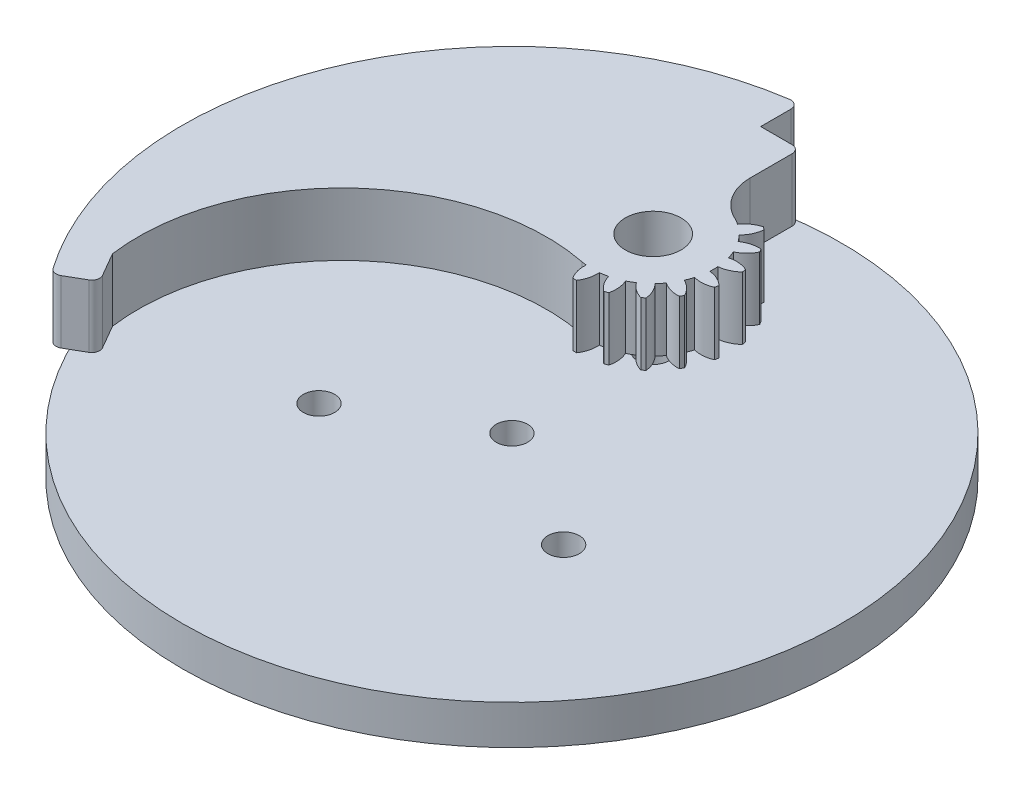
SolidWorks part; units mm, degrees
material "PE Low Density Film"
ref_plane "Front Plane" through (0, 0, 0) normal (0, 0, 1) x (1, 0, 0)
ref_plane "Top Plane" through (0, 0, 0) normal (0, 1, 0) x (1, 0, 0)
ref_plane "Right Plane" through (0, 0, 0) normal (1, 0, 0) x (0, 0, -1)
sketch "Sketch2" plane through (0, 0, 0) normal (0, 1, 0) x (1, 0, 0)
  line L0 (0, 18) -> (0, 0) construction
  line L1 (0, 0) -> (0, 18) construction
  circle A0 centre (0, 0) radius 42
  circle A1 centre (0, 0) radius 2
  circle A2 centre (0, 18) radius 2
  circle A3 centre (15.5885, -9) radius 2
  circle A4 centre (-15.5885, -9) radius 2
  dimension "D1" = 84
  dimension "D2" = 4
  dimension "D3" = 4
  dimension "D4" = 18
  dimension "D5" = 3
extrude "Boss-Extrude1" add sketch "Sketch2" along normal blind 5
sketch "Sketch3" plane through (0, 5, 0) normal (0, 1, 0) x (1, 0, 0)
  line L0 (0, 0) -> (0, 18) construction
sketch "Sketch5" plane through (0, 5, 0) normal (0, 1, 0) x (1, 0, 0)
  arc A72 (6.2374, 25.8163) -> (4.3083, 24.4409) centre (7.2464, 22.3606) ccw
  arc A73 (4.3083, 24.4409) -> (3.4238, 24.9516) centre (0, 18) ccw
  arc A74 (3.4238, 24.9516) -> (3.6504, 27.3099) centre (0.1532, 26.4558) ccw
  arc A75 (3.6504, 27.3099) -> (3.1879, 27.4783) centre (0, 18) ccw
  arc A76 (3.1879, 27.4783) -> (1.8456, 25.526) centre (5.318, 24.576) ccw
  arc A77 (1.8456, 25.526) -> (0.8398, 25.7034) centre (0, 18) ccw
  arc A78 (0.8398, 25.7034) -> (0.2461, 27.997) centre (-2.7481, 25.9983) ccw
  arc A79 (0.2461, 27.997) -> (-0.2461, 27.997) centre (0, 18) ccw
  arc A80 (-0.2461, 27.997) -> (-0.8398, 25.7034) centre (2.7481, 25.9983) ccw
  arc A81 (-0.8398, 25.7034) -> (-1.8456, 25.526) centre (0, 18) ccw
  arc A82 (-1.8456, 25.526) -> (-3.1879, 27.4783) centre (-5.318, 24.576) ccw
  arc A83 (-3.1879, 27.4783) -> (-3.6504, 27.3099) centre (0, 18) ccw
  arc A84 (-3.6504, 27.3099) -> (-3.4238, 24.9516) centre (-0.1532, 26.4558) ccw
  arc A85 (-3.4238, 24.9516) -> (-4.3083, 24.4409) centre (0, 18) ccw
  arc A86 (-4.3083, 24.4409) -> (-6.2374, 25.8163) centre (-7.2464, 22.3606) ccw
  arc A87 (-6.2374, 25.8163) -> (-6.6145, 25.4999) centre (0, 18) ccw
  arc A88 (-6.6145, 25.4999) -> (-5.5949, 23.3613) centre (-3.036, 25.8935) ccw
  arc A89 (-5.5949, 23.3613) -> (-6.2514, 22.579) centre (0, 18) ccw
  arc A90 (-6.2514, 22.579) -> (-8.5346, 23.2116) centre (-8.3008, 19.6192) ccw
  arc A91 (-8.5346, 23.2116) -> (-8.7807, 22.7854) centre (0, 18) ccw
  arc A92 (-8.7807, 22.7854) -> (-7.0912, 21.1244) centre (-5.5527, 24.3791) ccw
  arc A93 (-7.0912, 21.1244) -> (-7.4405, 20.1647) centre (0, 18) ccw
  arc A94 (-7.4405, 20.1647) -> (-9.8024, 19.9783) centre (-8.354, 16.6825) ccw
  arc A95 (-9.8024, 19.9783) -> (-9.8878, 19.4936) centre (0, 18) ccw
  arc A96 (-9.8878, 19.4936) -> (-7.7322, 18.5106) centre (-7.3996, 22.0952) ccw
  arc A97 (-7.7322, 18.5106) -> (-7.7322, 17.4894) centre (0, 18) ccw
  arc A98 (-7.7322, 17.4894) -> (-9.8878, 16.5064) centre (-7.3996, 13.9048) ccw
  arc A99 (-9.8878, 16.5064) -> (-9.8024, 16.0217) centre (0, 18) ccw
  arc A100 (-9.8024, 16.0217) -> (-7.4405, 15.8353) centre (-8.354, 19.3175) ccw
  arc A101 (-7.4405, 15.8353) -> (-7.0912, 14.8756) centre (0, 18) ccw
  arc A102 (-7.0912, 14.8756) -> (-8.7807, 13.2146) centre (-5.5527, 11.6209) ccw
  arc A103 (-8.7807, 13.2146) -> (-8.5346, 12.7884) centre (0, 18) ccw
  arc A104 (-8.5346, 12.7884) -> (-6.2514, 13.421) centre (-8.3008, 16.3808) ccw
  arc A105 (-6.2514, 13.421) -> (-5.5949, 12.6387) centre (0, 18) ccw
  arc A106 (-5.5949, 12.6387) -> (-6.6145, 10.5001) centre (-3.036, 10.1065) ccw
  arc A107 (-6.6145, 10.5001) -> (-6.2374, 10.1837) centre (0, 18) ccw
  arc A108 (-6.2374, 10.1837) -> (-4.3083, 11.5591) centre (-7.2464, 13.6394) ccw
  arc A109 (-4.3083, 11.5591) -> (-3.4238, 11.0484) centre (0, 18) ccw
  arc A110 (-3.4238, 11.0484) -> (-3.6504, 8.6901) centre (-0.1532, 9.5442) ccw
  arc A111 (-3.6504, 8.6901) -> (-3.1879, 8.5217) centre (0, 18) ccw
  arc A112 (-3.1879, 8.5217) -> (-1.8456, 10.474) centre (-5.318, 11.424) ccw
  arc A113 (-1.8456, 10.474) -> (-0.8398, 10.2966) centre (0, 18) ccw
  arc A114 (-0.8398, 10.2966) -> (-0.2461, 8.003) centre (2.7481, 10.0017) ccw
  arc A115 (-0.2461, 8.003) -> (0.2461, 8.003) centre (0, 18) ccw
  arc A116 (0.2461, 8.003) -> (0.8398, 10.2966) centre (-2.7481, 10.0017) ccw
  arc A117 (0.8398, 10.2966) -> (1.8456, 10.474) centre (0, 18) ccw
  arc A118 (1.8456, 10.474) -> (3.1879, 8.5217) centre (5.318, 11.424) ccw
  arc A119 (3.1879, 8.5217) -> (3.6504, 8.6901) centre (0, 18) ccw
  arc A120 (3.6504, 8.6901) -> (3.4238, 11.0484) centre (0.1532, 9.5442) ccw
  arc A121 (3.4238, 11.0484) -> (4.3083, 11.5591) centre (0, 18) ccw
  arc A122 (4.3083, 11.5591) -> (6.2374, 10.1837) centre (7.2464, 13.6394) ccw
  arc A123 (6.2374, 10.1837) -> (6.6145, 10.5001) centre (0, 18) ccw
  arc A124 (6.6145, 10.5001) -> (5.5949, 12.6387) centre (3.036, 10.1065) ccw
  arc A125 (5.5949, 12.6387) -> (6.2514, 13.421) centre (0, 18) ccw
  arc A126 (6.2514, 13.421) -> (8.5346, 12.7884) centre (8.3008, 16.3808) ccw
  arc A127 (8.5346, 12.7884) -> (8.7807, 13.2146) centre (0, 18) ccw
  arc A128 (8.7807, 13.2146) -> (7.0912, 14.8756) centre (5.5527, 11.6209) ccw
  arc A129 (7.0912, 14.8756) -> (7.4405, 15.8353) centre (0, 18) ccw
  arc A130 (7.4405, 15.8353) -> (9.8024, 16.0217) centre (8.354, 19.3175) ccw
  arc A131 (9.8024, 16.0217) -> (9.8878, 16.5064) centre (0, 18) ccw
  arc A132 (9.8878, 16.5064) -> (7.7322, 17.4894) centre (7.3996, 13.9048) ccw
  arc A133 (7.7322, 17.4894) -> (7.7322, 18.5106) centre (0, 18) ccw
  arc A134 (7.7322, 18.5106) -> (9.8878, 19.4936) centre (7.3996, 22.0952) ccw
  arc A135 (9.8878, 19.4936) -> (9.8024, 19.9783) centre (0, 18) ccw
  arc A136 (9.8024, 19.9783) -> (7.4405, 20.1647) centre (8.354, 16.6825) ccw
  arc A137 (7.4405, 20.1647) -> (7.0912, 21.1244) centre (0, 18) ccw
  arc A138 (7.0912, 21.1244) -> (8.7807, 22.7854) centre (5.5527, 24.3791) ccw
  arc A139 (8.7807, 22.7854) -> (8.5346, 23.2116) centre (0, 18) ccw
  arc A140 (8.5346, 23.2116) -> (6.2514, 22.579) centre (8.3008, 19.6192) ccw
  arc A141 (6.2514, 22.579) -> (5.5949, 23.3613) centre (0, 18) ccw
  arc A142 (5.5949, 23.3613) -> (6.6145, 25.4999) centre (3.036, 25.8935) ccw
  arc A143 (6.6145, 25.4999) -> (6.2374, 25.8163) centre (0, 18) ccw
  arc A144 (6.2374, 25.8163) -> (4.3083, 24.4409) centre (7.2464, 22.3606) ccw
  arc A145 (4.3083, 24.4409) -> (3.4238, 24.9516) centre (0, 18) ccw
  arc A146 (3.4238, 24.9516) -> (3.6504, 27.3099) centre (0.1532, 26.4558) ccw
  arc A147 (3.6504, 27.3099) -> (3.1879, 27.4783) centre (0, 18) ccw
  arc A148 (3.1879, 27.4783) -> (1.8456, 25.526) centre (5.318, 24.576) ccw
  arc A149 (1.8456, 25.526) -> (0.8398, 25.7034) centre (0, 18) ccw
  arc A150 (0.8398, 25.7034) -> (0.2461, 27.997) centre (-2.7481, 25.9983) ccw
  arc A151 (0.2461, 27.997) -> (-0.2461, 27.997) centre (0, 18) ccw
  arc A152 (-0.2461, 27.997) -> (-0.8398, 25.7034) centre (2.7481, 25.9983) ccw
  arc A153 (-0.8398, 25.7034) -> (-1.8456, 25.526) centre (0, 18) ccw
  arc A154 (-1.8456, 25.526) -> (-3.1879, 27.4783) centre (-5.318, 24.576) ccw
  arc A155 (-3.1879, 27.4783) -> (-3.6504, 27.3099) centre (0, 18) ccw
  arc A156 (-3.6504, 27.3099) -> (-3.4238, 24.9516) centre (-0.1532, 26.4558) ccw
  arc A157 (-3.4238, 24.9516) -> (-4.3083, 24.4409) centre (0, 18) ccw
  arc A158 (-4.3083, 24.4409) -> (-6.2374, 25.8163) centre (-7.2464, 22.3606) ccw
  arc A159 (-6.2374, 25.8163) -> (-6.6145, 25.4999) centre (0, 18) ccw
  arc A160 (-6.6145, 25.4999) -> (-5.5949, 23.3613) centre (-3.036, 25.8935) ccw
  arc A161 (-5.5949, 23.3613) -> (-6.2514, 22.579) centre (0, 18) ccw
  arc A162 (-6.2514, 22.579) -> (-8.5346, 23.2116) centre (-8.3008, 19.6192) ccw
  arc A163 (-8.5346, 23.2116) -> (-8.7807, 22.7854) centre (0, 18) ccw
  arc A164 (-8.7807, 22.7854) -> (-7.0912, 21.1244) centre (-5.5527, 24.3791) ccw
  arc A165 (-7.0912, 21.1244) -> (-7.4405, 20.1647) centre (0, 18) ccw
  arc A166 (-7.4405, 20.1647) -> (-9.8024, 19.9783) centre (-8.354, 16.6825) ccw
  arc A167 (-9.8024, 19.9783) -> (-9.8878, 19.4936) centre (0, 18) ccw
  arc A168 (-9.8878, 19.4936) -> (-7.7322, 18.5106) centre (-7.3996, 22.0952) ccw
  arc A169 (-7.7322, 18.5106) -> (-7.7322, 17.4894) centre (0, 18) ccw
  arc A170 (-7.7322, 17.4894) -> (-9.8878, 16.5064) centre (-7.3996, 13.9048) ccw
  arc A171 (-9.8878, 16.5064) -> (-9.8024, 16.0217) centre (0, 18) ccw
  arc A172 (-9.8024, 16.0217) -> (-7.4405, 15.8353) centre (-8.354, 19.3175) ccw
  arc A173 (-7.4405, 15.8353) -> (-7.0912, 14.8756) centre (0, 18) ccw
  arc A174 (-7.0912, 14.8756) -> (-8.7807, 13.2146) centre (-5.5527, 11.6209) ccw
  arc A175 (-8.7807, 13.2146) -> (-8.5346, 12.7884) centre (0, 18) ccw
  arc A176 (-8.5346, 12.7884) -> (-6.2514, 13.421) centre (-8.3008, 16.3808) ccw
  arc A177 (-6.2514, 13.421) -> (-5.5949, 12.6387) centre (0, 18) ccw
  arc A178 (-5.5949, 12.6387) -> (-6.6145, 10.5001) centre (-3.036, 10.1065) ccw
  arc A179 (-6.6145, 10.5001) -> (-6.2374, 10.1837) centre (0, 18) ccw
  arc A180 (-6.2374, 10.1837) -> (-4.3083, 11.5591) centre (-7.2464, 13.6394) ccw
  arc A181 (-4.3083, 11.5591) -> (-3.4238, 11.0484) centre (0, 18) ccw
  arc A182 (-3.4238, 11.0484) -> (-3.6504, 8.6901) centre (-0.1532, 9.5442) ccw
  arc A183 (-3.6504, 8.6901) -> (-3.1879, 8.5217) centre (0, 18) ccw
  arc A184 (-3.1879, 8.5217) -> (-1.8456, 10.474) centre (-5.318, 11.424) ccw
  arc A185 (-1.8456, 10.474) -> (-0.8398, 10.2966) centre (0, 18) ccw
  arc A186 (-0.8398, 10.2966) -> (-0.2461, 8.003) centre (2.7481, 10.0017) ccw
  arc A187 (-0.2461, 8.003) -> (0.2461, 8.003) centre (0, 18) ccw
  arc A188 (0.2461, 8.003) -> (0.8398, 10.2966) centre (-2.7481, 10.0017) ccw
  arc A189 (0.8398, 10.2966) -> (1.8456, 10.474) centre (0, 18) ccw
  arc A190 (1.8456, 10.474) -> (3.1879, 8.5217) centre (5.318, 11.424) ccw
  arc A191 (3.1879, 8.5217) -> (3.6504, 8.6901) centre (0, 18) ccw
  arc A192 (3.6504, 8.6901) -> (3.4238, 11.0484) centre (0.1532, 9.5442) ccw
  arc A193 (3.4238, 11.0484) -> (4.3083, 11.5591) centre (0, 18) ccw
  arc A194 (4.3083, 11.5591) -> (6.2374, 10.1837) centre (7.2464, 13.6394) ccw
  arc A195 (6.2374, 10.1837) -> (6.6145, 10.5001) centre (0, 18) ccw
  arc A196 (6.6145, 10.5001) -> (5.5949, 12.6387) centre (3.036, 10.1065) ccw
  arc A197 (5.5949, 12.6387) -> (6.2514, 13.421) centre (0, 18) ccw
  arc A198 (6.2514, 13.421) -> (8.5346, 12.7884) centre (8.3008, 16.3808) ccw
  arc A199 (8.5346, 12.7884) -> (8.7807, 13.2146) centre (0, 18) ccw
  arc A200 (8.7807, 13.2146) -> (7.0912, 14.8756) centre (5.5527, 11.6209) ccw
  arc A201 (7.0912, 14.8756) -> (7.4405, 15.8353) centre (0, 18) ccw
  arc A202 (7.4405, 15.8353) -> (9.8024, 16.0217) centre (8.354, 19.3175) ccw
  arc A203 (9.8024, 16.0217) -> (9.8878, 16.5064) centre (0, 18) ccw
  arc A204 (9.8878, 16.5064) -> (7.7322, 17.4894) centre (7.3996, 13.9048) ccw
  arc A205 (7.7322, 17.4894) -> (7.7322, 18.5106) centre (0, 18) ccw
  arc A206 (7.7322, 18.5106) -> (9.8878, 19.4936) centre (7.3996, 22.0952) ccw
  arc A207 (9.8878, 19.4936) -> (9.8024, 19.9783) centre (0, 18) ccw
  arc A208 (9.8024, 19.9783) -> (7.4405, 20.1647) centre (8.354, 16.6825) ccw
  arc A209 (7.4405, 20.1647) -> (7.0912, 21.1244) centre (0, 18) ccw
  arc A210 (7.0912, 21.1244) -> (8.7807, 22.7854) centre (5.5527, 24.3791) ccw
  arc A211 (8.7807, 22.7854) -> (8.5346, 23.2116) centre (0, 18) ccw
  arc A212 (8.5346, 23.2116) -> (6.2514, 22.579) centre (8.3008, 19.6192) ccw
  arc A213 (6.2514, 22.579) -> (5.5949, 23.3613) centre (0, 18) ccw
  arc A214 (5.5949, 23.3613) -> (6.6145, 25.4999) centre (3.036, 25.8935) ccw
  arc A215 (6.6145, 25.4999) -> (6.2374, 25.8163) centre (0, 18) ccw
  dimension "D1" = 0
sketch "Sketch6" plane through (0, 5, 0) normal (0, 1, 0) x (1, 0, 0)
  line L0 (-36.3731, -21) -> (0, 0) construction
  line L1 (0, 0) -> (0, 42) construction
  line L2 (-33.9137, -24.7762) -> (-30.0166, -22.5262)
  line L3 (-30.0166, -22.5262) -> (-32.2666, -18.6291)
  line L4 (-5, 41.7013) -> (-5, 36.7013)
  line L5 (-5, 36.7013) -> (0, 36.7013)
  line L6 (0, 36.7013) -> (0, 30.3704)
  arc A0 (-33.9137, -24.7762) -> (-5, 41.7013) centre (0, 0) cw
  circle A1 centre (0, 0) radius 42 construction
  circle A3 centre (15.5885, -9) radius 10 construction
  circle A4 centre (-15.5885, -9) radius 10 construction
  circle A6 centre (0, 0) radius 10 construction
  circle A11 centre (0, 18) radius 3.55
  arc A18 (-32.2666, -18.6291) -> (-1.4936, 10.3963) centre (-6.505, -15.1162) cw
  arc A19 (0, 30.3704) -> (3.4238, 24.9516) centre (6, 30.3704) ccw
  arc A20 (-0.8398, 10.2966) -> (-1.4936, 10.3963) centre (0, 18) cw
  arc A72 (5.5949, 23.3613) -> (6.6145, 25.4999) centre (3.036, 25.8935) ccw
  arc A73 (6.6145, 25.4999) -> (6.2374, 25.8163) centre (0, 18) ccw
  arc A74 (6.2374, 25.8163) -> (4.3083, 24.4409) centre (7.2464, 22.3606) ccw
  arc A75 (4.3083, 24.4409) -> (3.4238, 24.9516) centre (0, 18) ccw
  arc A76 (3.4238, 24.9516) -> (3.6504, 27.3099) centre (0.1532, 26.4558) ccw
  arc A77 (3.6504, 27.3099) -> (3.1879, 27.4783) centre (0, 18) ccw
  arc A78 (3.1879, 27.4783) -> (1.8456, 25.526) centre (5.318, 24.576) ccw
  arc A79 (1.8456, 25.526) -> (0.8398, 25.7034) centre (0, 18) ccw
  arc A80 (0.8398, 25.7034) -> (0.2461, 27.997) centre (-2.7481, 25.9983) ccw
  arc A81 (0.2461, 27.997) -> (-0.2461, 27.997) centre (0, 18) ccw
  arc A82 (-0.2461, 27.997) -> (-0.8398, 25.7034) centre (2.7481, 25.9983) ccw
  arc A83 (-0.8398, 25.7034) -> (-1.8456, 25.526) centre (0, 18) ccw
  arc A84 (-1.8456, 25.526) -> (-3.1879, 27.4783) centre (-5.318, 24.576) ccw
  arc A85 (-3.1879, 27.4783) -> (-3.6504, 27.3099) centre (0, 18) ccw
  arc A86 (-3.6504, 27.3099) -> (-3.4238, 24.9516) centre (-0.1532, 26.4558) ccw
  arc A87 (-3.4238, 24.9516) -> (-4.3083, 24.4409) centre (0, 18) ccw
  arc A88 (-4.3083, 24.4409) -> (-6.2374, 25.8163) centre (-7.2464, 22.3606) ccw
  arc A89 (-6.2374, 25.8163) -> (-6.6145, 25.4999) centre (0, 18) ccw
  arc A90 (-6.6145, 25.4999) -> (-5.5949, 23.3613) centre (-3.036, 25.8935) ccw
  arc A91 (-5.5949, 23.3613) -> (-6.2514, 22.579) centre (0, 18) ccw
  arc A92 (-6.2514, 22.579) -> (-8.5346, 23.2116) centre (-8.3008, 19.6192) ccw
  arc A93 (-8.5346, 23.2116) -> (-8.7807, 22.7854) centre (0, 18) ccw
  arc A94 (-8.7807, 22.7854) -> (-7.0912, 21.1244) centre (-5.5527, 24.3791) ccw
  arc A95 (-7.0912, 21.1244) -> (-7.4405, 20.1647) centre (0, 18) ccw
  arc A96 (-7.4405, 20.1647) -> (-9.8024, 19.9783) centre (-8.354, 16.6825) ccw
  arc A97 (-9.8024, 19.9783) -> (-9.8878, 19.4936) centre (0, 18) ccw
  arc A98 (-9.8878, 19.4936) -> (-7.7322, 18.5106) centre (-7.3996, 22.0952) ccw
  arc A99 (-7.7322, 18.5106) -> (-7.7322, 17.4894) centre (0, 18) ccw
  arc A100 (-7.7322, 17.4894) -> (-9.8878, 16.5064) centre (-7.3996, 13.9048) ccw
  arc A101 (-9.8878, 16.5064) -> (-9.8024, 16.0217) centre (0, 18) ccw
  arc A102 (-9.8024, 16.0217) -> (-7.4405, 15.8353) centre (-8.354, 19.3175) ccw
  arc A103 (-7.4405, 15.8353) -> (-7.0912, 14.8756) centre (0, 18) ccw
  arc A104 (-7.0912, 14.8756) -> (-8.7807, 13.2146) centre (-5.5527, 11.6209) ccw
  arc A105 (-8.7807, 13.2146) -> (-8.5346, 12.7884) centre (0, 18) ccw
  arc A106 (-8.5346, 12.7884) -> (-6.2514, 13.421) centre (-8.3008, 16.3808) ccw
  arc A107 (-6.2514, 13.421) -> (-5.5949, 12.6387) centre (0, 18) ccw
  arc A108 (-5.5949, 12.6387) -> (-6.6145, 10.5001) centre (-3.036, 10.1065) ccw
  arc A109 (-6.6145, 10.5001) -> (-6.2374, 10.1837) centre (0, 18) ccw
  arc A110 (-6.2374, 10.1837) -> (-4.3083, 11.5591) centre (-7.2464, 13.6394) ccw
  arc A111 (-4.3083, 11.5591) -> (-3.4238, 11.0484) centre (0, 18) ccw
  arc A112 (-3.4238, 11.0484) -> (-3.6504, 8.6901) centre (-0.1532, 9.5442) ccw
  arc A113 (-3.6504, 8.6901) -> (-3.1879, 8.5217) centre (0, 18) ccw
  arc A114 (-3.1879, 8.5217) -> (-1.8456, 10.474) centre (-5.318, 11.424) ccw
  arc A115 (-1.8456, 10.474) -> (-0.8398, 10.2966) centre (0, 18) ccw
  arc A116 (-0.8398, 10.2966) -> (-0.2461, 8.003) centre (2.7481, 10.0017) ccw
  arc A117 (-0.2461, 8.003) -> (0.2461, 8.003) centre (0, 18) ccw
  arc A118 (0.2461, 8.003) -> (0.8398, 10.2966) centre (-2.7481, 10.0017) ccw
  arc A119 (0.8398, 10.2966) -> (1.8456, 10.474) centre (0, 18) ccw
  arc A120 (1.8456, 10.474) -> (3.1879, 8.5217) centre (5.318, 11.424) ccw
  arc A121 (3.1879, 8.5217) -> (3.6504, 8.6901) centre (0, 18) ccw
  arc A122 (3.6504, 8.6901) -> (3.4238, 11.0484) centre (0.1532, 9.5442) ccw
  arc A123 (3.4238, 11.0484) -> (4.3083, 11.5591) centre (0, 18) ccw
  arc A124 (4.3083, 11.5591) -> (6.2374, 10.1837) centre (7.2464, 13.6394) ccw
  arc A125 (6.2374, 10.1837) -> (6.6145, 10.5001) centre (0, 18) ccw
  arc A126 (6.6145, 10.5001) -> (5.5949, 12.6387) centre (3.036, 10.1065) ccw
  arc A127 (5.5949, 12.6387) -> (6.2514, 13.421) centre (0, 18) ccw
  arc A128 (6.2514, 13.421) -> (8.5346, 12.7884) centre (8.3008, 16.3808) ccw
  arc A129 (8.5346, 12.7884) -> (8.7807, 13.2146) centre (0, 18) ccw
  arc A130 (8.7807, 13.2146) -> (7.0912, 14.8756) centre (5.5527, 11.6209) ccw
  arc A131 (7.0912, 14.8756) -> (7.4405, 15.8353) centre (0, 18) ccw
  arc A132 (7.4405, 15.8353) -> (9.8024, 16.0217) centre (8.354, 19.3175) ccw
  arc A133 (9.8024, 16.0217) -> (9.8878, 16.5064) centre (0, 18) ccw
  arc A134 (9.8878, 16.5064) -> (7.7322, 17.4894) centre (7.3996, 13.9048) ccw
  arc A135 (7.7322, 17.4894) -> (7.7322, 18.5106) centre (0, 18) ccw
  arc A136 (7.7322, 18.5106) -> (9.8878, 19.4936) centre (7.3996, 22.0952) ccw
  arc A137 (9.8878, 19.4936) -> (9.8024, 19.9783) centre (0, 18) ccw
  arc A138 (9.8024, 19.9783) -> (7.4405, 20.1647) centre (8.354, 16.6825) ccw
  arc A139 (7.4405, 20.1647) -> (7.0912, 21.1244) centre (0, 18) ccw
  arc A140 (7.0912, 21.1244) -> (8.7807, 22.7854) centre (5.5527, 24.3791) ccw
  arc A141 (8.7807, 22.7854) -> (8.5346, 23.2116) centre (0, 18) ccw
  arc A142 (8.5346, 23.2116) -> (6.2514, 22.579) centre (8.3008, 19.6192) ccw
  arc A143 (6.2514, 22.579) -> (5.5949, 23.3613) centre (0, 18) ccw
  arc A144 (5.5949, 23.3613) -> (6.6145, 25.4999) centre (3.036, 25.8935) ccw
  arc A145 (6.6145, 25.4999) -> (6.2374, 25.8163) centre (0, 18) ccw
  arc A146 (6.2374, 25.8163) -> (4.3083, 24.4409) centre (7.2464, 22.3606) ccw
  arc A147 (4.3083, 24.4409) -> (3.4238, 24.9516) centre (0, 18) ccw
  arc A148 (3.4238, 24.9516) -> (3.6504, 27.3099) centre (0.1532, 26.4558) ccw construction
  arc A149 (3.6504, 27.3099) -> (3.1879, 27.4783) centre (0, 18) ccw construction
  arc A150 (3.1879, 27.4783) -> (1.8456, 25.526) centre (5.318, 24.576) ccw construction
  arc A151 (1.8456, 25.526) -> (0.8398, 25.7034) centre (0, 18) ccw construction
  arc A152 (0.8398, 25.7034) -> (0.2461, 27.997) centre (-2.7481, 25.9983) ccw construction
  arc A153 (0.2461, 27.997) -> (-0.2461, 27.997) centre (0, 18) ccw construction
  arc A154 (-0.2461, 27.997) -> (-0.8398, 25.7034) centre (2.7481, 25.9983) ccw construction
  arc A155 (-0.8398, 25.7034) -> (-1.8456, 25.526) centre (0, 18) ccw construction
  arc A156 (-1.8456, 25.526) -> (-3.1879, 27.4783) centre (-5.318, 24.576) ccw construction
  arc A157 (-3.1879, 27.4783) -> (-3.6504, 27.3099) centre (0, 18) ccw construction
  arc A158 (-3.6504, 27.3099) -> (-3.4238, 24.9516) centre (-0.1532, 26.4558) ccw construction
  arc A159 (-3.4238, 24.9516) -> (-4.3083, 24.4409) centre (0, 18) ccw construction
  arc A160 (-4.3083, 24.4409) -> (-6.2374, 25.8163) centre (-7.2464, 22.3606) ccw construction
  arc A161 (-6.2374, 25.8163) -> (-6.6145, 25.4999) centre (0, 18) ccw construction
  arc A162 (-6.6145, 25.4999) -> (-5.5949, 23.3613) centre (-3.036, 25.8935) ccw construction
  arc A163 (-5.5949, 23.3613) -> (-6.2514, 22.579) centre (0, 18) ccw construction
  arc A164 (-6.2514, 22.579) -> (-8.5346, 23.2116) centre (-8.3008, 19.6192) ccw construction
  arc A165 (-8.5346, 23.2116) -> (-8.7807, 22.7854) centre (0, 18) ccw construction
  arc A166 (-8.7807, 22.7854) -> (-7.0912, 21.1244) centre (-5.5527, 24.3791) ccw construction
  arc A167 (-7.0912, 21.1244) -> (-7.4405, 20.1647) centre (0, 18) ccw construction
  arc A168 (-7.4405, 20.1647) -> (-9.8024, 19.9783) centre (-8.354, 16.6825) ccw construction
  arc A169 (-9.8024, 19.9783) -> (-9.8878, 19.4936) centre (0, 18) ccw construction
  arc A170 (-9.8878, 19.4936) -> (-7.7322, 18.5106) centre (-7.3996, 22.0952) ccw construction
  arc A171 (-7.7322, 18.5106) -> (-7.7322, 17.4894) centre (0, 18) ccw construction
  arc A172 (-7.7322, 17.4894) -> (-9.8878, 16.5064) centre (-7.3996, 13.9048) ccw construction
  arc A173 (-9.8878, 16.5064) -> (-9.8024, 16.0217) centre (0, 18) ccw construction
  arc A174 (-9.8024, 16.0217) -> (-7.4405, 15.8353) centre (-8.354, 19.3175) ccw construction
  arc A175 (-7.4405, 15.8353) -> (-7.0912, 14.8756) centre (0, 18) ccw construction
  arc A176 (-7.0912, 14.8756) -> (-8.7807, 13.2146) centre (-5.5527, 11.6209) ccw construction
  arc A177 (-8.7807, 13.2146) -> (-8.5346, 12.7884) centre (0, 18) ccw construction
  arc A178 (-8.5346, 12.7884) -> (-6.2514, 13.421) centre (-8.3008, 16.3808) ccw construction
  arc A179 (-6.2514, 13.421) -> (-5.5949, 12.6387) centre (0, 18) ccw construction
  arc A180 (-5.5949, 12.6387) -> (-6.6145, 10.5001) centre (-3.036, 10.1065) ccw construction
  arc A181 (-6.6145, 10.5001) -> (-6.2374, 10.1837) centre (0, 18) ccw construction
  arc A182 (-6.2374, 10.1837) -> (-4.3083, 11.5591) centre (-7.2464, 13.6394) ccw construction
  arc A183 (-4.3083, 11.5591) -> (-3.4238, 11.0484) centre (0, 18) ccw construction
  arc A184 (-3.4238, 11.0484) -> (-3.6504, 8.6901) centre (-0.1532, 9.5442) ccw construction
  arc A185 (-3.6504, 8.6901) -> (-3.1879, 8.5217) centre (0, 18) ccw construction
  arc A186 (-3.1879, 8.5217) -> (-1.8456, 10.474) centre (-5.318, 11.424) ccw construction
  arc A187 (-1.8456, 10.474) -> (-0.8398, 10.2966) centre (0, 18) ccw construction
  arc A188 (-0.8398, 10.2966) -> (-0.2461, 8.003) centre (2.7481, 10.0017) ccw
  arc A189 (-0.2461, 8.003) -> (0.2461, 8.003) centre (0, 18) ccw
  arc A190 (0.2461, 8.003) -> (0.8398, 10.2966) centre (-2.7481, 10.0017) ccw
  arc A191 (0.8398, 10.2966) -> (1.8456, 10.474) centre (0, 18) ccw
  arc A192 (1.8456, 10.474) -> (3.1879, 8.5217) centre (5.318, 11.424) ccw
  arc A193 (3.1879, 8.5217) -> (3.6504, 8.6901) centre (0, 18) ccw
  arc A194 (3.6504, 8.6901) -> (3.4238, 11.0484) centre (0.1532, 9.5442) ccw
  arc A195 (3.4238, 11.0484) -> (4.3083, 11.5591) centre (0, 18) ccw
  arc A196 (4.3083, 11.5591) -> (6.2374, 10.1837) centre (7.2464, 13.6394) ccw
  arc A197 (6.2374, 10.1837) -> (6.6145, 10.5001) centre (0, 18) ccw
  arc A198 (6.6145, 10.5001) -> (5.5949, 12.6387) centre (3.036, 10.1065) ccw
  arc A199 (5.5949, 12.6387) -> (6.2514, 13.421) centre (0, 18) ccw
  arc A200 (6.2514, 13.421) -> (8.5346, 12.7884) centre (8.3008, 16.3808) ccw
  arc A201 (8.5346, 12.7884) -> (8.7807, 13.2146) centre (0, 18) ccw
  arc A202 (8.7807, 13.2146) -> (7.0912, 14.8756) centre (5.5527, 11.6209) ccw
  arc A203 (7.0912, 14.8756) -> (7.4405, 15.8353) centre (0, 18) ccw
  arc A204 (7.4405, 15.8353) -> (9.8024, 16.0217) centre (8.354, 19.3175) ccw
  arc A205 (9.8024, 16.0217) -> (9.8878, 16.5064) centre (0, 18) ccw
  arc A206 (9.8878, 16.5064) -> (7.7322, 17.4894) centre (7.3996, 13.9048) ccw
  arc A207 (7.7322, 17.4894) -> (7.7322, 18.5106) centre (0, 18) ccw
  arc A208 (7.7322, 18.5106) -> (9.8878, 19.4936) centre (7.3996, 22.0952) ccw
  arc A209 (9.8878, 19.4936) -> (9.8024, 19.9783) centre (0, 18) ccw
  arc A210 (9.8024, 19.9783) -> (7.4405, 20.1647) centre (8.354, 16.6825) ccw
  arc A211 (7.4405, 20.1647) -> (7.0912, 21.1244) centre (0, 18) ccw
  arc A212 (7.0912, 21.1244) -> (8.7807, 22.7854) centre (5.5527, 24.3791) ccw
  arc A213 (8.7807, 22.7854) -> (8.5346, 23.2116) centre (0, 18) ccw
  arc A214 (8.5346, 23.2116) -> (6.2514, 22.579) centre (8.3008, 19.6192) ccw
  arc A215 (6.2514, 22.579) -> (5.5949, 23.3613) centre (0, 18) ccw
  dimension "D4" = 20
  dimension "D5" = 4.5
  dimension "D3" = 4.5
  dimension "D8" = 26
  dimension "D9" = 6
  dimension "D10" = 7.1
  dimension "D2" = 120
  dimension "D6" = 5
  dimension "D7" = 5
  dimension "D1" = 0
extrude "Boss-Extrude2" add sketch "Sketch6" along normal blind 8 from offset 5
fillet "Fillet1" radius 1 4 edges at (0, 14, -36.7013) (-5, 14, -41.7013) (-30.0166, 14, 22.5262) (-33.9137, 14, 24.7762)
